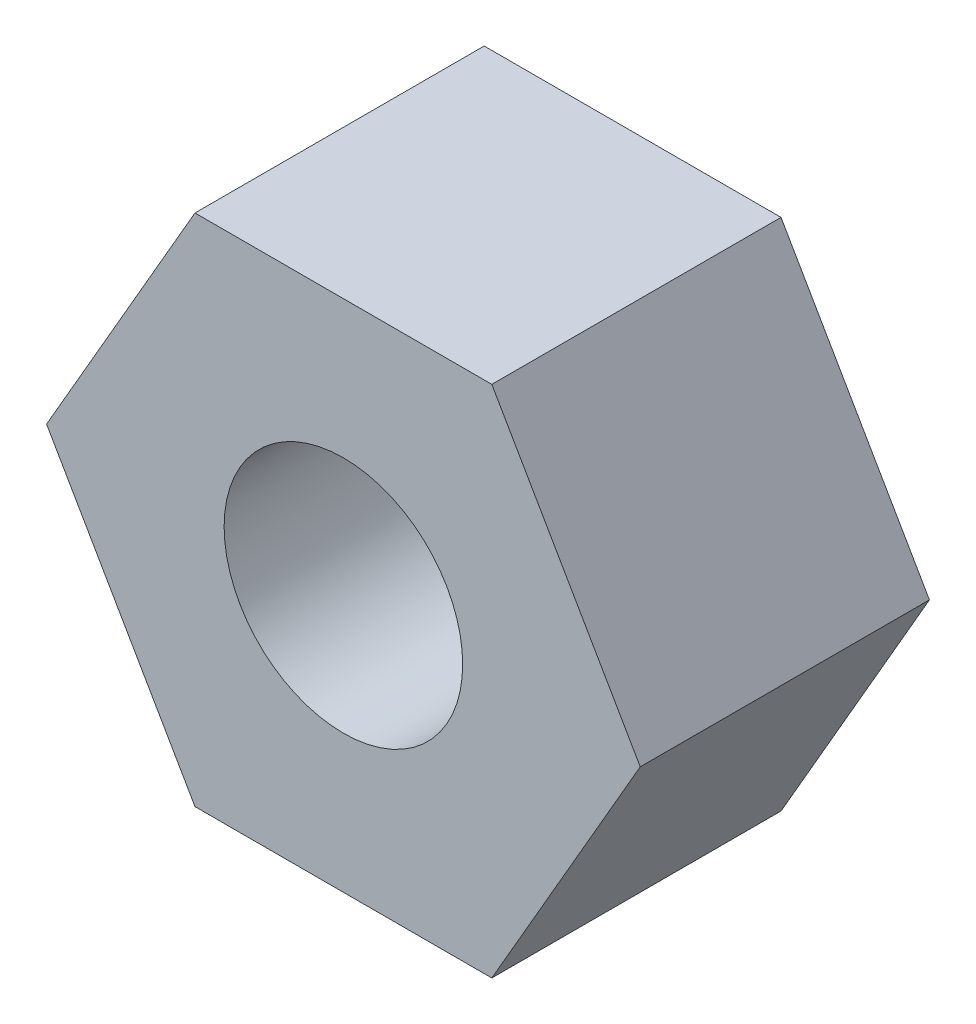
SolidWorks part; units mm, degrees
ref_plane "Front Plane" through (0, 0, 0) normal (0, 0, 1) x (1, 0, 0)
ref_plane "Top Plane" through (0, 0, 0) normal (0, 1, 0) x (1, 0, 0)
ref_plane "Right Plane" through (0, 0, 0) normal (1, 0, 0) x (0, 0, -1)
sketch "Sketch1" plane through (0, 0, 0) normal (0, 0, 1) x (1, 0, 0)
  line L1 (3.6662, 0) -> (1.8331, 3.175)
  line L2 (1.8331, 3.175) -> (-1.8331, 3.175)
  line L3 (-1.8331, 3.175) -> (-3.6662, 0)
  line L4 (-3.6662, 0) -> (-1.8331, -3.175)
  line L5 (-1.8331, -3.175) -> (1.8331, -3.175)
  line L6 (1.8331, -3.175) -> (3.6662, 0)
  circle A0 centre (0, 0) radius 3.175 construction
  circle A1 centre (0, 0) radius 1.4732
extrude "Extrude1" add sketch "Sketch1" along normal blind 3.5719
